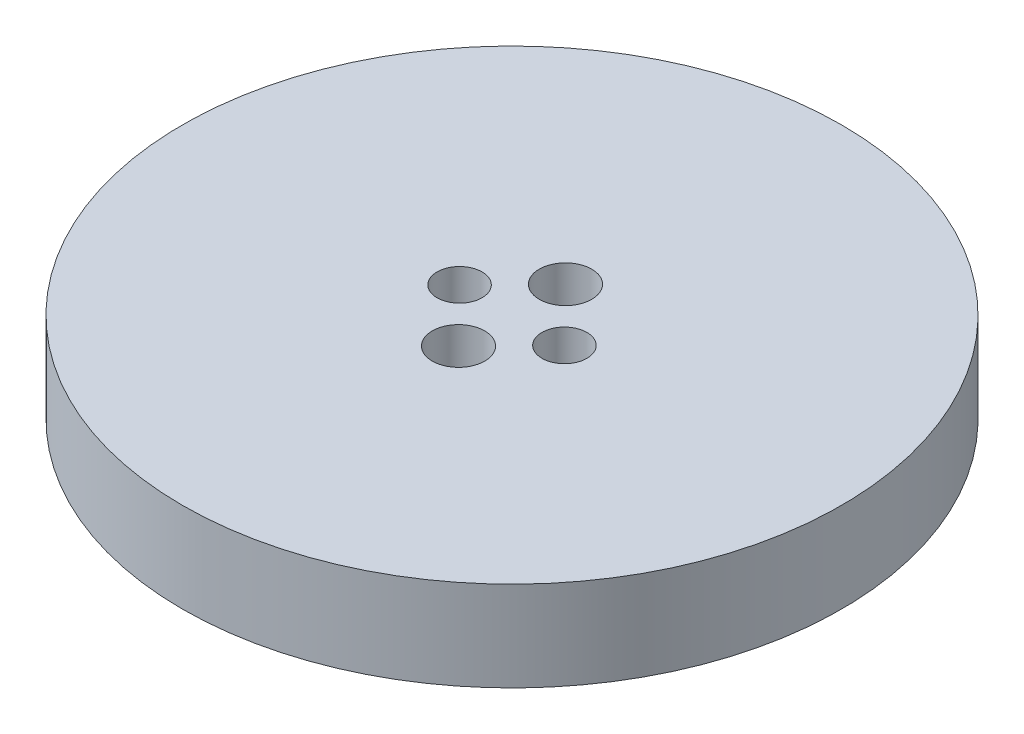
SolidWorks part; units mm, degrees
ref_plane "Plan de face" through (0, 0, 0) normal (0, 0, 1) x (1, 0, 0)
ref_plane "Plan de dessus" through (0, 0, 0) normal (0, 1, 0) x (1, 0, 0)
ref_plane "Plan de droite" through (0, 0, 0) normal (1, 0, 0) x (0, 0, -1)
sketch "Esquisse1" plane through (0, 0, 0) normal (0, 1, 0) x (1, 0, 0)
  line L0 (-3.5, 0) -> (3.5, 0) construction
  circle A0 centre (0, 0) radius 22
  circle A2 centre (-3.5, 0) radius 1.5
  circle A3 centre (3.5, 0) radius 1.5
  circle A13 centre (0, 3.5707) radius 1.75
  circle A14 centre (0, -3.5707) radius 1.75
  point P12 (0.1512, -4.1397)
  dimension "D1" = 44
  dimension "D4" = 7
  dimension "D5" = 3
  dimension "D6" = 3
  dimension "D12" = 3.5
  dimension "D13" = 3.5
extrude "Boss.-Extru.1" add sketch "Esquisse1" along normal blind 6
